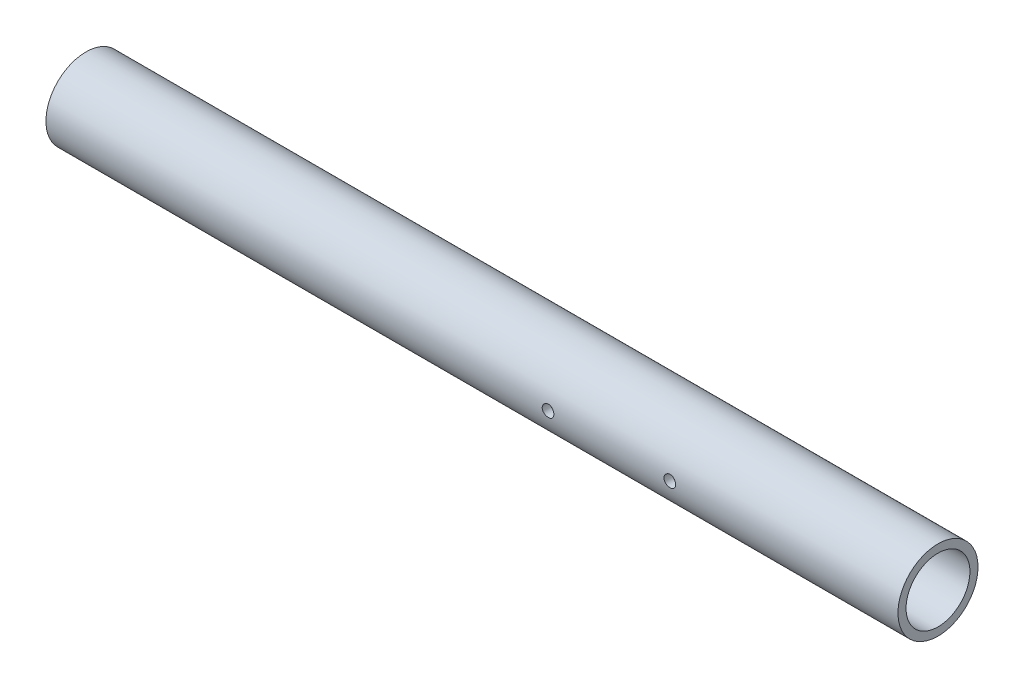
SolidWorks part; units mm, degrees
material "6061-T6 (SS)"
ref_plane "Front Plane" through (0, 0, 0) normal (0, 0, 1) x (1, 0, 0)
ref_plane "Top Plane" through (0, 0, 0) normal (0, 1, 0) x (1, 0, 0)
ref_plane "Right Plane" through (0, 0, 0) normal (1, 0, 0) x (0, 0, -1)
sketch "Sketch1" plane through (0, 0, 0) normal (1, 0, 0) x (0, 0, -1)
  circle A0 centre (0, 0) radius 16.7005
  circle A1 centre (0, 0) radius 13.335
  dimension "D1" = 33.401
  dimension "D2" = 26.67
extrude "Boss-Extrude1" add sketch "Sketch1" along normal blind 355.6
sketch "Sketch2" plane through (0, 0, 0) normal (0, 0, 1) x (1, 0, 0)
  line L0 (0, 16.7005) -> (0, -16.7005) construction
  circle A0 centre (209.55, 0) radius 2.4257
  circle A1 centre (260.35, 0) radius 2.4257
  dimension "D1" = 4.8514
  dimension "D2" = 209.55
  dimension "D3" = 50.8
extrude "Cut-Extrude1" cut sketch "Sketch2" against normal through all both and the other way through all
